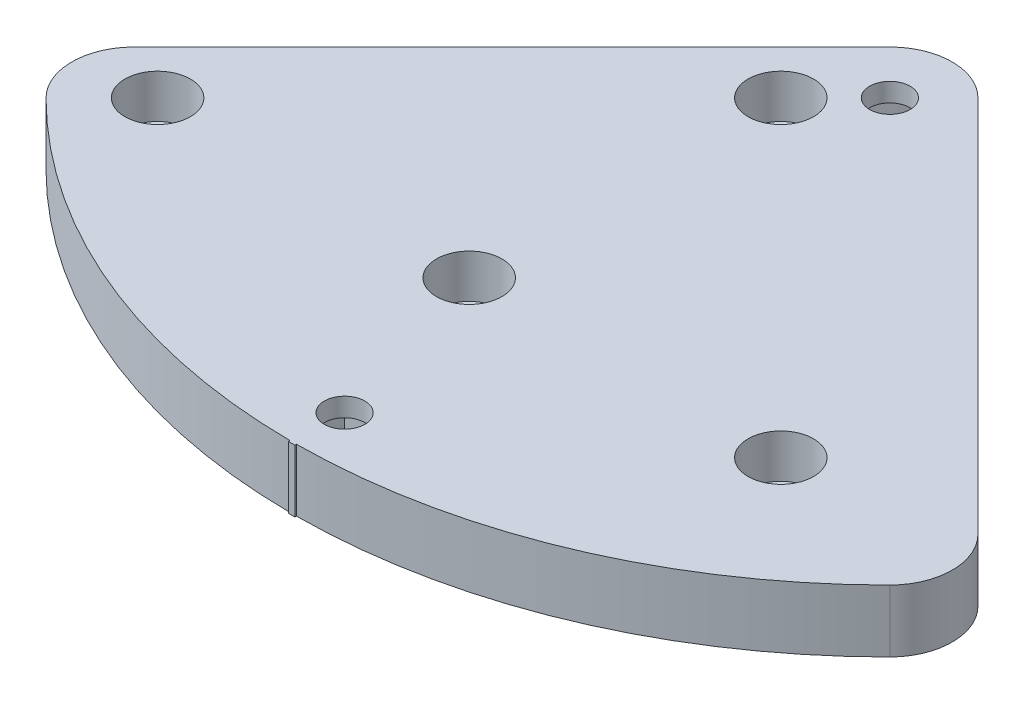
SolidWorks part; units mm, degrees
ref_plane "정면" through (0, 0, 0) normal (0, 0, 1) x (1, 0, 0)
ref_plane "윗면" through (0, 0, 0) normal (0, 1, 0) x (1, 0, 0)
ref_plane "우측면" through (0, 0, 0) normal (1, 0, 0) x (0, 0, -1)
sketch "스케치1" plane through (0, 0, 0) normal (0, 1, 0) x (1, 0, 0)
  line L0 (0, 0) -> (67.7055, -67.7055) construction
  line L1 (0, 0) -> (-67.7055, -67.7055) construction
  line L2 (0, 0) -> (0, -95.75) construction
  line L3 (-7.0711, 7.0711) -> (-67.7055, -53.5633)
  line L4 (7.0711, 7.0711) -> (67.7055, -53.5633)
  arc A0 (-67.7055, -67.7055) -> (67.7055, -67.7055) centre (0, 0) ccw
  circle A1 centre (-8.75, -58.75) radius 3.2
  arc A2 (-67.7055, -53.5633) -> (-67.7055, -67.7055) centre (-60.6344, -60.6344) ccw
  arc A3 (67.7055, -67.7055) -> (67.7055, -53.5633) centre (60.6344, -60.6344) ccw
  circle A4 centre (-8.75, -8.75) radius 3.2
  arc A5 (7.0711, 7.0711) -> (-7.0711, 7.0711) centre (0, 0) ccw
  circle A7 centre (-58.75, -58.75) radius 3.2
  circle A8 centre (41.25, -58.75) radius 3.2
  point P5 (-8.75, -8.75)
  point P17 (0, -87.5)
  point P20 (0, 0)
  point P21 (0, 0)
  dimension "D1" = 8.75
  dimension "D7" = 10
  dimension "D8" = 191.5
  dimension "D11" = 87.5
  dimension "D14" = 6.4
  dimension "D4" = 8.75
  dimension "D9" = 45
  dimension "D10" = 45
  dimension "D12" = 50
  dimension "D13" = 100
extrude "보스-돌출1" add sketch "스케치1" along normal blind 10
sketch "스케치2" plane through (0, 10, 0) normal (0, 1, 0) x (1, 0, 0)
  circle A0 centre (-8.75, -8.75) radius 5.25
  circle A1 centre (-58.75, -58.75) radius 5.25
  circle A4 centre (-8.75, -8.75) radius 3.2 construction
  circle A5 centre (-58.75, -58.75) radius 3.2 construction
  circle A7 centre (-8.75, -58.75) radius 3.2 construction
  circle A8 centre (41.25, -58.75) radius 3.2 construction
  circle A12 centre (41.25, -58.75) radius 5.25
  circle A14 centre (-8.75, -58.75) radius 5.25
  point P6 (0, 0)
  point P7 (0, 0)
  point P11 (0, 0)
  dimension "D1" = 10.5
extrude "컷-돌출1" cut sketch "스케치2" against normal offset from surface (7 mm away) 3 up to face at (0, 0, 42.2518)
sketch "스케치3" plane through (0, 10, 0) normal (0, 1, 0) x (1, 0, 0)
  circle A0 centre (0, 0) radius 3.25
  circle A1 centre (0, -87.5) radius 3.25
  point P2 (0, 0)
  point P6 (0, 0)
  dimension "D2" = 6.5
  dimension "D3" = 87.5
extrude "컷-돌출2" cut sketch "스케치3" against normal up to surface (10 mm away) up to face at (0, 0, 42.2518)
sketch "스케치4" plane through (0, 0, 0) normal (0, -1, 0) x (1, 0, 0)
  line L1 (0, 7.3539) -> (-7.3539, 0)
  line L2 (0, 7.3539) -> (7.3539, 0)
  line L3 (7.3539, 0) -> (0, -7.3539)
  line L4 (-7.3539, 0) -> (0, -7.3539)
  line L5 (-5.2, 82.3) -> (5.2, 82.3)
  line L6 (-5.2, 82.3) -> (-5.2, 92.7)
  line L7 (-5.2, 92.7) -> (5.2, 92.7)
  line L8 (5.2, 82.3) -> (5.2, 92.7)
  circle A0 centre (0, 87.5) radius 3.25 construction
  circle A1 centre (0, 0) radius 3.25
  circle A2 centre (0, 0) radius 3.25 construction
  circle A3 centre (0, 87.5) radius 3.25
  point P5 (0, 0)
  point P6 (0, 0)
  point P8 (0, 0)
  point P9 (-5.8855, 1.6182)
  point P16 (0, 92.7)
  point P17 (6.761, -0.1915)
  point P18 (5.2, 87.5)
  point P19 (0, 80)
  point P20 (21.6714, 4.8095)
  point P25 (-5.2, 5.2)
  point P26 (0, 0)
  point P27 (0, 82.3)
  point P28 (5.2, 92.7)
  point P29 (5.2, 92.7)
  point P30 (5.2, 92.7)
  point P31 (0, 0)
  point P32 (0, 0)
  point P33 (7.2019, 81.9778)
  dimension "D1" = 10.4
extrude "컷-돌출3" cut sketch "스케치4" against normal offset from surface (7 mm away) 3 up to face at (0, 10, 90.75)
sketch "스케치5" plane through (0, 10, 0) normal (0, 1, 0) x (1, 0, 0)
  line L0 (0.5053, -95.9987) -> (0.5, -94.9987)
  line L1 (0, 0) -> (0.5, -94.9987) construction
  line L2 (-0.5053, -95.9987) -> (-0.5, -94.9987)
  line L5 (0, 0) -> (0, -87.5) construction
  line L6 (0, 0) -> (-0.5, -94.9987) construction
  arc A0 (-0.5053, -95.9987) -> (0.5053, -95.9987) centre (0, 0) ccw
  arc A1 (-0.5, -94.9987) -> (0.5, -94.9987) centre (0, 0) ccw
  point P10 (0, 0)
  point P14 (0, 0)
  point P16 (0, 0)
  point P17 (0, 0)
  dimension "D1" = 192
  dimension "D2" = 95
  dimension "D3" = 0.5
  dimension "D4" = 0.5
extrude "보스-돌출2" add sketch "스케치5" against normal up to surface (10 mm away) up to face at (0, 0, 87.5)
fillet "필렛1" [suppressed] radius 10
